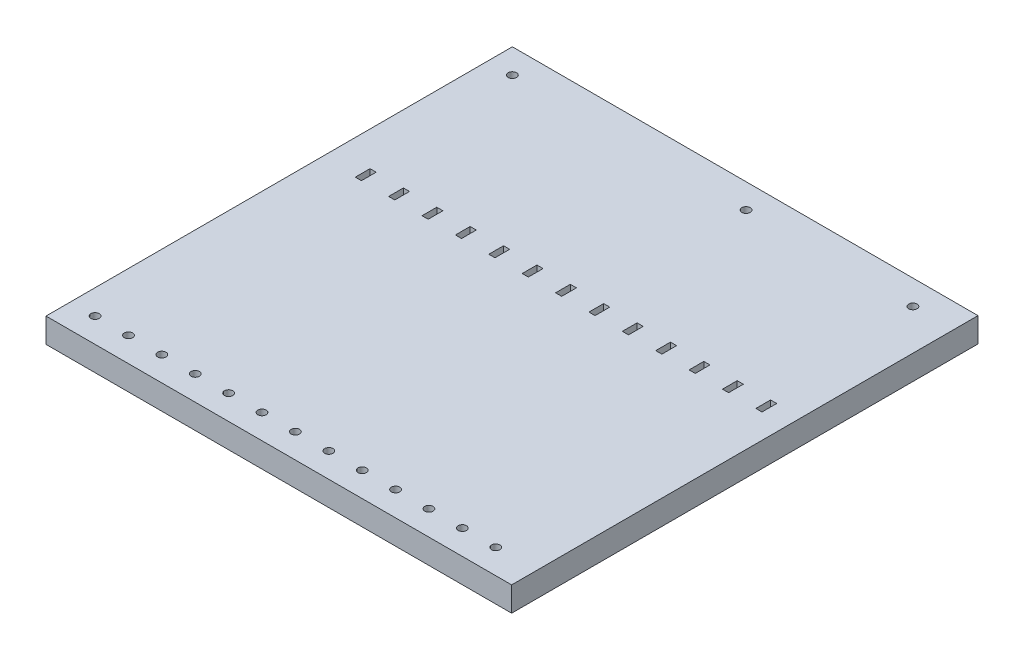
SolidWorks part; units mm, degrees
ref_plane "Front Plane" through (0, 0, 0) normal (0, 0, 1) x (1, 0, 0)
ref_plane "Top Plane" through (0, 0, 0) normal (0, 1, 0) x (1, 0, 0)
ref_plane "Right Plane" through (0, 0, 0) normal (1, 0, 0) x (0, 0, -1)
sketch "Sketch1" plane through (0, 0, 0) normal (0, 1, 0) x (1, 0, 0)
  line L0 (0, 0) -> (0, 105) construction
  line L1 (0, 105) -> (4, 105) construction
  line L2 (0, 105) -> (0, 145) construction
  line L3 (4, 102) -> (6.5, 102)
  line L4 (4, 102) -> (4, 108)
  line L5 (4, 108) -> (6.5, 108)
  line L6 (6.5, 102) -> (6.5, 108)
  line L7 (0, 145) -> (0, 170) construction
  line L8 (0, 0) -> (13.6, 0) construction
  line L9 (4, 102) -> (6.5, 108) construction
  line L10 (5.25, 105) -> (18.85, 105) construction
  line L15 (179.7, 108) -> (169.7, 108) construction
  line L20 (17.6, 102) -> (17.6, 108)
  line L25 (17.6, 102) -> (20.1, 102)
  line L30 (20.1, 102) -> (20.1, 108)
  line L35 (17.6, 108) -> (20.1, 108)
  line L40 (17.6, 102) -> (20.1, 108) construction
  line L45 (31.2, 102) -> (31.2, 108)
  line L50 (31.2, 102) -> (33.7, 102)
  line L55 (33.7, 102) -> (33.7, 108)
  line L60 (31.2, 108) -> (33.7, 108)
  line L65 (31.2, 102) -> (33.7, 108) construction
  line L66 (-10, 0) -> (0, 0) construction
  line L67 (-10, -10) -> (179.7, -10)
  line L68 (-10, -10) -> (-10, 180)
  line L69 (-10, 180) -> (179.7, 180)
  line L70 (179.7, -10) -> (179.7, 180)
  line L71 (0, 0) -> (0, -10) construction
  line L72 (44.8, 102) -> (44.8, 108)
  line L73 (0, 170) -> (0, 180) construction
  line L74 (44.8, 102) -> (47.3, 102)
  line L75 (47.3, 102) -> (47.3, 108)
  line L76 (44.8, 108) -> (47.3, 108)
  line L77 (44.8, 102) -> (47.3, 108) construction
  line L78 (58.4, 102) -> (58.4, 108)
  line L79 (58.4, 102) -> (60.9, 102)
  line L80 (60.9, 102) -> (60.9, 108)
  line L81 (58.4, 108) -> (60.9, 108)
  line L82 (58.4, 102) -> (60.9, 108) construction
  line L83 (72, 102) -> (72, 108)
  line L84 (72, 102) -> (74.5, 102)
  line L85 (74.5, 102) -> (74.5, 108)
  line L86 (72, 108) -> (74.5, 108)
  line L87 (72, 102) -> (74.5, 108) construction
  line L88 (85.6, 102) -> (85.6, 108)
  line L89 (85.6, 102) -> (88.1, 102)
  line L90 (88.1, 102) -> (88.1, 108)
  line L91 (85.6, 108) -> (88.1, 108)
  line L92 (85.6, 102) -> (88.1, 108) construction
  line L93 (99.2, 102) -> (99.2, 108)
  line L94 (99.2, 102) -> (101.7, 102)
  line L95 (101.7, 102) -> (101.7, 108)
  line L96 (99.2, 108) -> (101.7, 108)
  line L97 (99.2, 102) -> (101.7, 108) construction
  line L98 (112.8, 102) -> (112.8, 108)
  line L99 (112.8, 102) -> (115.3, 102)
  line L100 (115.3, 102) -> (115.3, 108)
  line L101 (112.8, 108) -> (115.3, 108)
  line L102 (112.8, 102) -> (115.3, 108) construction
  line L103 (126.4, 102) -> (126.4, 108)
  line L104 (126.4, 102) -> (128.9, 102)
  line L105 (128.9, 102) -> (128.9, 108)
  line L106 (126.4, 108) -> (128.9, 108)
  line L107 (126.4, 102) -> (128.9, 108) construction
  line L108 (140, 102) -> (140, 108)
  line L109 (140, 102) -> (142.5, 102)
  line L110 (142.5, 102) -> (142.5, 108)
  line L111 (140, 108) -> (142.5, 108)
  line L112 (140, 102) -> (142.5, 108) construction
  line L113 (153.6, 102) -> (153.6, 108)
  line L114 (153.6, 102) -> (156.1, 102)
  line L115 (156.1, 102) -> (156.1, 108)
  line L116 (153.6, 108) -> (156.1, 108)
  line L117 (153.6, 102) -> (156.1, 108) construction
  line L118 (167.2, 102) -> (167.2, 108)
  line L119 (167.2, 102) -> (169.7, 102)
  line L120 (169.7, 102) -> (169.7, 108)
  line L121 (167.2, 108) -> (169.7, 108)
  line L122 (167.2, 102) -> (169.7, 108) construction
  line L123 (0, 170) -> (13.6, 170) construction
  line L124 (163.2, 0) -> (163.2, 170) construction
  circle A0 centre (0, 0) radius 1.5 construction
  circle A25 centre (0, 0) radius 1.7
  circle A26 centre (0, 170) radius 1.7
  circle A27 centre (13.6, 0) radius 1.7
  circle A28 centre (27.2, 0) radius 1.7
  circle A29 centre (40.8, 0) radius 1.7
  circle A30 centre (54.4, 0) radius 1.7
  circle A31 centre (68, 0) radius 1.7
  circle A32 centre (81.6, 0) radius 1.7
  circle A33 centre (95.2, 0) radius 1.7
  circle A34 centre (108.8, 0) radius 1.7
  circle A35 centre (122.4, 0) radius 1.7
  circle A36 centre (136, 0) radius 1.7
  circle A37 centre (149.6, 0) radius 1.7
  circle A38 centre (163.2, 0) radius 1.7
  circle A39 centre (13.6, 170) radius 1.7 [skipped]
  circle A40 centre (27.2, 170) radius 1.7 [skipped]
  circle A41 centre (40.8, 170) radius 1.7 [skipped]
  circle A42 centre (54.4, 170) radius 1.7 [skipped]
  circle A43 centre (68, 170) radius 1.7 [skipped]
  circle A44 centre (81.6, 170) radius 1.7 [skipped]
  circle A45 centre (95.2, 170) radius 1.7
  circle A46 centre (108.8, 170) radius 1.7 [skipped]
  circle A47 centre (122.4, 170) radius 1.7 [skipped]
  circle A48 centre (136, 170) radius 1.7 [skipped]
  circle A49 centre (149.6, 170) radius 1.7 [skipped]
  circle A50 centre (163.2, 170) radius 1.7
  point P9 (4, 105)
  point P15 (18.85, 105)
  dimension "D2" = 3
  dimension "D1" = 105
  dimension "D3" = 4
  dimension "D4" = 6
  dimension "D5" = 2.5
  dimension "D6" = 145
  dimension "D7" = 25
  dimension "D9" = 13.6
  dimension "D11" = 10
  dimension "D8" = 0.2
  dimension "D10" = 13
  dimension "D12" = 13
  dimension "D13" = 13
extrude "Boss-Extrude1" add sketch "Sketch1" against normal blind 10
equation "\"Tolerance\"=0.2"
equation "\"D8@Sketch1\"=\"Tolerance\""
